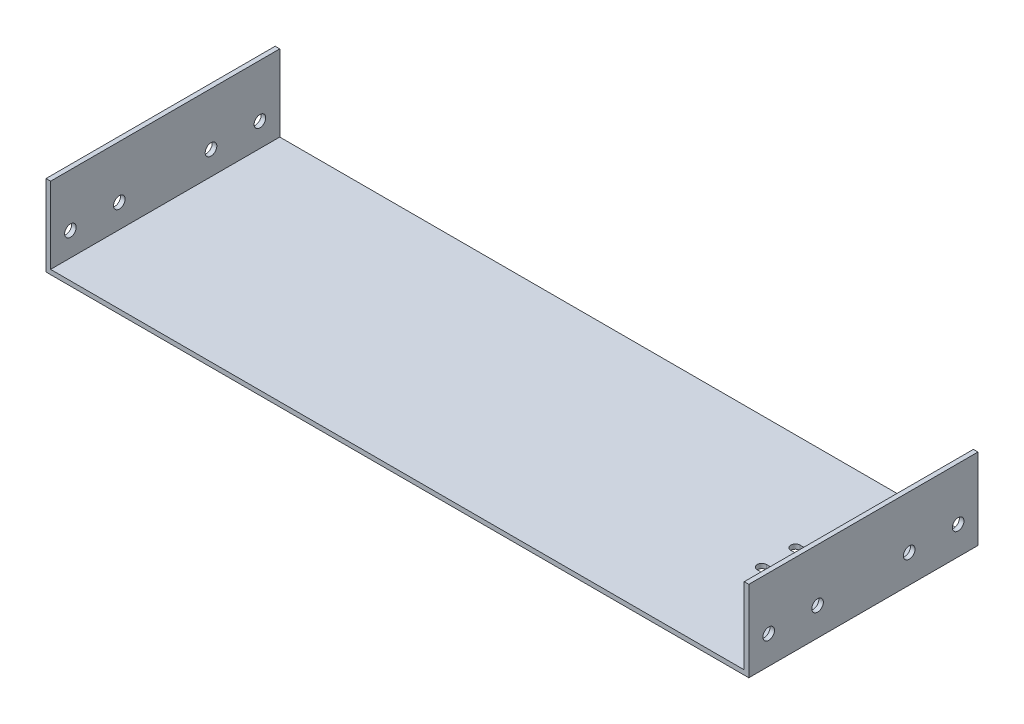
SolidWorks part; units mm, degrees
ref_plane "Front Plane" through (0, 0, 0) normal (0, 0, 1) x (1, 0, 0)
ref_plane "Top Plane" through (0, 0, 0) normal (0, 1, 0) x (1, 0, 0)
ref_plane "Right Plane" through (0, 0, 0) normal (1, 0, 0) x (0, 0, -1)
sketch "Sketch1" plane through (0, 0, 0) normal (0, 1, 0) x (1, 0, 0)
  line L1 (-230, 75) -> (230, 75)
  line L2 (-230, 75) -> (-230, -75)
  line L3 (-230, -75) -> (230, -75)
  line L4 (230, 75) -> (230, -75)
  line L5 (-230, 75) -> (230, -75) construction
  line L6 (-230, -75) -> (230, 75) construction
  point P0 (0, 0)
  dimension "D1" = 460
  dimension "D2" = 150
extrude "Boss-Extrude1" add sketch "Sketch1" along normal blind 3
sketch "Sketch2" plane through (0, 3, 0) normal (0, 1, 0) x (1, 0, 0)
  line L0 (-230, -75) -> (230, -75) construction
  line L1 (-230, 75) -> (-227, 75)
  line L2 (-230, 75) -> (-230, -75)
  line L3 (-230, -75) -> (-227, -75)
  line L4 (-227, 75) -> (-227, -75)
  line L6 (230, 75) -> (227, 75)
  line L7 (230, 75) -> (230, -75)
  line L8 (230, -75) -> (227, -75)
  line L9 (227, 75) -> (227, -75)
  dimension "D1" = 3
  dimension "D2" = 3
extrude "Boss-Extrude2" add sketch "Sketch2" along normal blind 50
sketch "Sketch4" plane through (-227, 0, 0) normal (1, 0, 0) x (0, 0, -1)
  circle A0 centre (62, 18.5) radius 3.8
  circle A1 centre (30, 18.5) radius 3.8
  circle A2 centre (-62, 18.5) radius 3.8
  circle A3 centre (-30, 18.5) radius 3.8
extrude "Cut-Extrude1" cut sketch "Sketch4" against normal through all both and the other way through all
sketch "Sketch5" plane through (0, 3, 0) normal (0, 1, 0) x (1, 0, 0)
  line L1 (174.5, 8) -> (204.5, 8)
  line L2 (174.5, 8) -> (174.5, 14)
  line L3 (174.5, 14) -> (204.5, 14)
  line L4 (204.5, 8) -> (204.5, 14)
  line L5 (204.5, -14) -> (174.5, -14)
  line L6 (204.5, -14) -> (204.5, -8)
  line L7 (204.5, -8) -> (174.5, -8)
  line L8 (174.5, -14) -> (174.5, -8)
  circle A0 centre (204.5, 11) radius 3
  circle A1 centre (174.5, 11) radius 3
  circle A2 centre (174.5, -11) radius 3
  circle A3 centre (204.5, -11) radius 3
extrude "Cut-Extrude2" cut sketch "Sketch5" against normal blind 10 contours L8 A2 | L8 A2 | A3 L7 A2 L5 | L6 A3 | L6 A3 | L4 A0 | L4 A0 | A1 L1 A0 L3 | L2 A1 | L2 A1
